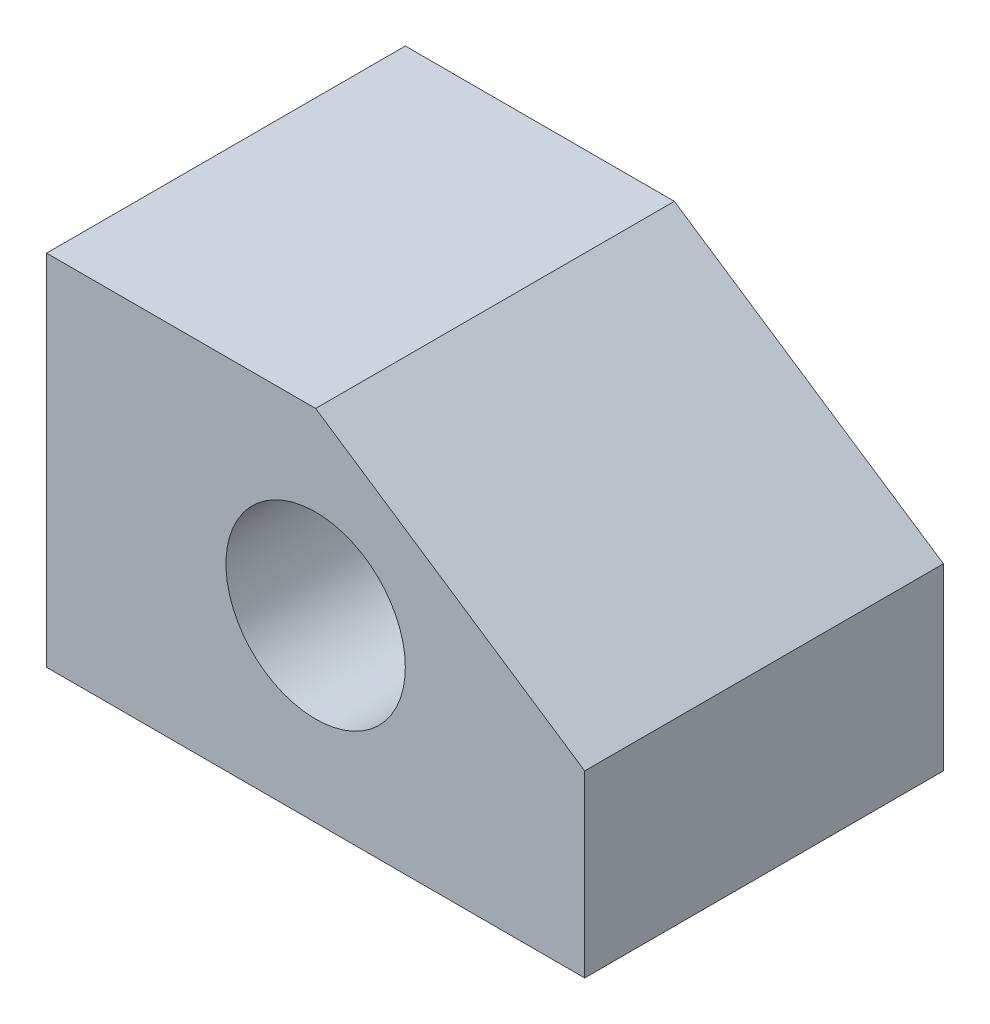
SolidWorks part; units mm, degrees
ref_plane "Front Plane" through (0, 0, 0) normal (0, 0, 1) x (1, 0, 0)
ref_plane "Top Plane" through (0, 0, 0) normal (0, 1, 0) x (1, 0, 0)
ref_plane "Right Plane" through (0, 0, 0) normal (1, 0, 0) x (0, 0, -1)
sketch "Sketch2" plane through (0, 0, 0) normal (0, 0, 1) x (1, 0, 0)
  line L0 (0, 0) -> (30, 0)
  line L1 (0, 0) -> (0, 20)
  line L2 (0, 20) -> (15, 20)
  line L3 (30, 0) -> (30, 10)
  line L4 (15, 20) -> (30, 10)
  point P8 (-135.3869, -5.6664)
  point P9 (0, 0)
extrude "Boss-Extrude1" add sketch "Sketch2" against normal blind 20 contours L1 L2 L4 L3 L0
sketch "Sketch6" plane through (0, 0, 0) normal (0, 0, 1) x (1, 0, 0)
sketch "Sketch7" plane through (0, 0, 0) normal (0, 0, 1) x (1, 0, 0)
  circle A0 centre (15, 10) radius 5
  point P2 (0, 0)
  point P4 (0, 0)
  point P6 (0, 0)
  dimension "D1" = 15
  dimension "D2" = 10
extrude "Cut-Extrude1" cut sketch "Sketch7" against normal blind 20 contours A0
